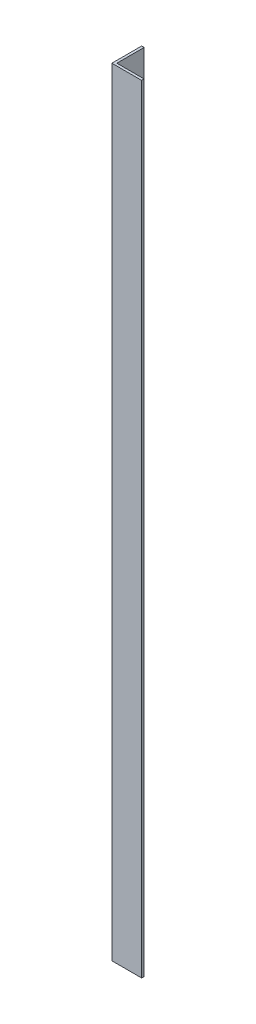
SolidWorks part; units mm, degrees
ref_plane "Front Plane" through (0, 0, 0) normal (0, 0, 1) x (1, 0, 0)
ref_plane "Top Plane" through (0, 0, 0) normal (0, 1, 0) x (1, 0, 0)
ref_plane "Right Plane" through (0, 0, 0) normal (1, 0, 0) x (0, 0, -1)
sketch "Sketch1" plane through (0, 0, 0) normal (0, 1, 0) x (1, 0, 0)
  line L0 (0, 0) -> (0, 19.15)
  line L1 (0, 19.15) -> (1.6, 19.15)
  line L2 (1.6, 19.15) -> (1.6, 1.6)
  line L3 (1.6, 1.6) -> (19.15, 1.6)
  line L4 (19.15, 1.6) -> (19.15, 0)
  line L5 (19.15, 0) -> (0, 0)
  dimension "D1" = 19.15
  dimension "D2" = 1.6
extrude "Boss-Extrude1" add sketch "Sketch1" along normal blind 500
